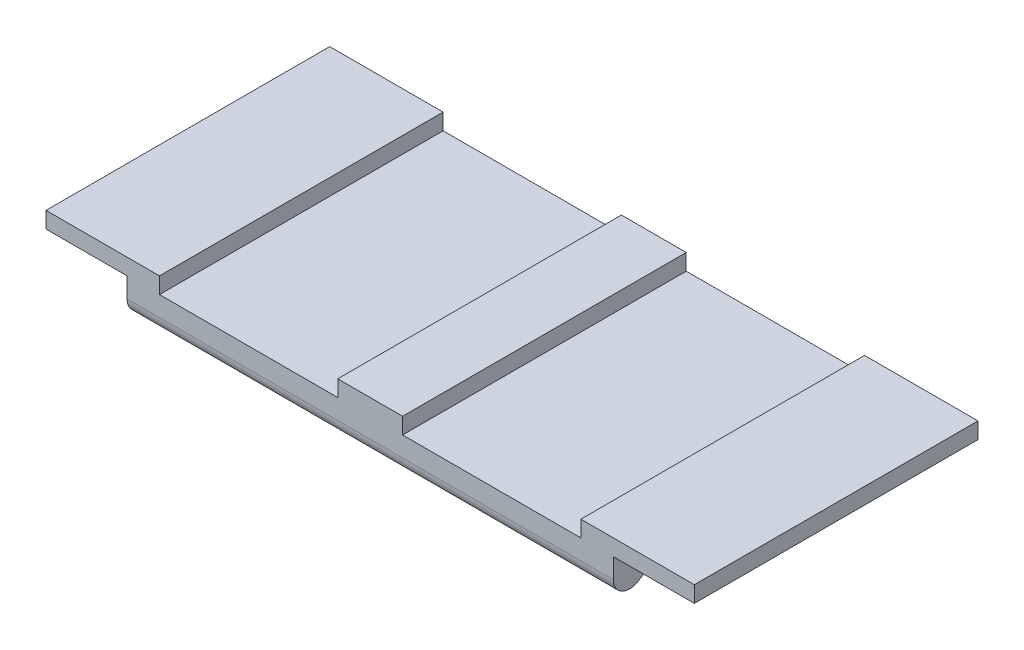
SolidWorks part; units mm, degrees
ref_plane "Front Plane" through (0, 0, 0) normal (0, 0, 1) x (1, 0, 0)
ref_plane "Top Plane" through (0, 0, 0) normal (0, 1, 0) x (1, 0, 0)
ref_plane "Right Plane" through (0, 0, 0) normal (1, 0, 0) x (0, 0, -1)
sketch "Sketch1" plane through (0, 0, 0) normal (0, 1, 0) x (1, 0, 0)
  line L1 (30, -17.5) -> (-30, -17.5)
  line L2 (30, -17.5) -> (30, 17.5)
  line L3 (30, 17.5) -> (-30, 17.5)
  line L4 (-30, -17.5) -> (-30, 17.5)
  line L5 (30, -17.5) -> (-30, 17.5) construction
  line L6 (30, 17.5) -> (-30, -17.5) construction
  point P0 (0, 0)
  dimension "D1" = 35
  dimension "D2" = 60
extrude "Boss-Extrude1" add sketch "Sketch1" against normal blind 8
sketch "Sketch2" plane through (30, 0, 0) normal (1, 0, 0) x (0, 0, -1)
  line L0 (-17.5, -8) -> (-12.5, -5)
  line L1 (-12.5, -5) -> (12.5, -5)
  line L2 (0, -5) -> (0, -8)
  line L3 (17.5, -8) -> (12.5, -5)
  line L4 (17.5, 0) -> (-17.5, 0)
  line L5 (-17.5, 0) -> (-17.5, -8)
  line L6 (-17.5, -8) -> (17.5, -8)
  line L7 (17.5, -8) -> (17.5, 0)
  line L8 (17.5, 0) -> (-17.5, 0)
  line L9 (-17.5, 0) -> (-17.5, -8)
  line L10 (-17.5, -8) -> (17.5, -8)
  line L11 (17.5, -8) -> (17.5, 0)
  line M7 (-17.5, -8) -> (17.5, -8)
  dimension "D2" = 5
  dimension "D3" = 3
  dimension "D1" = 0
extrude "Cut-Extrude1" cut sketch "Sketch2" against normal through all and the other way through all contours L2 L1 L0 M7 | L3 L1 L2 M7
fillet "Fillet1" radius 2 4 edges at (0, -5, 12.5) (0, -5, -12.5) (0, -8, -17.5) (0, -8, 17.5)
sketch "Sketch3" plane through (0, 0, 17.5) normal (0, 0, 1) x (1, 0, 0)
  line L0 (-30, 0) -> (30, 0) construction
  line L1 (-26, 2) -> (-4, 2)
  line L2 (-26, 2) -> (-26, -2)
  line L3 (-26, -2) -> (-4, -2)
  line L4 (-30, 0) -> (-30, -4.4676)
  line L5 (-30, -4.4676) -> (30, -4.4676)
  line L6 (30, -4.4676) -> (30, 0)
  line L7 (30, 0) -> (-30, 0)
  line L8 (-30, 0) -> (-30, -4.4676)
  line L9 (-30, -4.4676) -> (30, -4.4676)
  line L10 (30, -4.4676) -> (30, 0)
  line L11 (30, 0) -> (-30, 0)
  line L12 (-4, 2) -> (-4, -2)
  line L13 (-26, 2) -> (-4, -2) construction
  line L14 (-26, -2) -> (-4, 2) construction
  line L15 (0, 0) -> (0, -4.4676)
  line L16 (26, -2) -> (4, 2) construction
  line L17 (26, 2) -> (4, -2) construction
  line L18 (4, 2) -> (4, -2)
  line L19 (26, -2) -> (4, -2)
  line L20 (26, 2) -> (26, -2)
  line L21 (26, 2) -> (4, 2)
  point P2 (-15, 0)
  point P13 (0, 0)
  point P18 (15, 0)
  dimension "D2" = 22
  dimension "D3" = 4
  dimension "D4" = 15
  dimension "D1" = 0
extrude "Cut-Extrude2" cut sketch "Sketch3" against normal through all contours L12 L11 L2 L3 | L20 L11 L18 L19
sketch "Sketch5" plane through (-30, 0, 0) normal (-1, 0, 0) x (0, 0, 1)
  line L1 (-17.5, 0) -> (17.5, 0)
  line L2 (-17.5, 0) -> (-17.5, -2)
  line L3 (-17.5, -2) -> (17.5, -2)
  line L4 (17.5, 0) -> (17.5, -2)
  line L6 (-17.5, 0) -> (-17.5, -4.4676)
  line L7 (-14.471, -6.1826) -> (-12.975, -5.285)
  line L8 (-11.946, -5) -> (11.946, -5)
  line L9 (12.975, -5.285) -> (14.471, -6.1826)
  line L10 (17.5, -4.4676) -> (17.5, 0)
  line L11 (17.5, 0) -> (-17.5, 0)
  line L12 (-17.5, 0) -> (-17.5, -4.4676)
  line L13 (-14.471, -6.1826) -> (-12.975, -5.285)
  line L14 (-11.946, -5) -> (11.946, -5)
  line L15 (12.975, -5.285) -> (14.471, -6.1826)
  line L16 (17.5, -4.4676) -> (17.5, 0)
  line L17 (17.5, 0) -> (-17.5, 0)
  arc A4 (-17.5, -4.4676) -> (-14.471, -6.1826) centre (-15.5, -4.4676) ccw
  arc A5 (-11.946, -5) -> (-12.975, -5.285) centre (-11.946, -7) ccw
  arc A6 (12.975, -5.285) -> (11.946, -5) centre (11.946, -7) ccw
  arc A7 (14.471, -6.1826) -> (17.5, -4.4676) centre (15.5, -4.4676) ccw
  arc A8 (-17.5, -4.4676) -> (-14.471, -6.1826) centre (-15.5, -4.4676) ccw
  arc A9 (-11.946, -5) -> (-12.975, -5.285) centre (-11.946, -7) ccw
  arc A10 (12.975, -5.285) -> (11.946, -5) centre (11.946, -7) ccw
  arc A11 (14.471, -6.1826) -> (17.5, -4.4676) centre (15.5, -4.4676) ccw
  line M13 (-17.5, 0) -> (-17.5, -4.4676)
  line M21 (17.5, -4.4676) -> (17.5, 0)
  line M22 (17.5, 0) -> (-17.5, 0)
  dimension "D2" = 2
  dimension "D1" = 0
extrude "Boss-Extrude2" add sketch "Sketch5" along normal blind 10 contours L3 M13 M21 M22
mirror "Mirror1" about plane through (0, 0, 0) normal (1, 0, 0) of "Boss-Extrude2"
